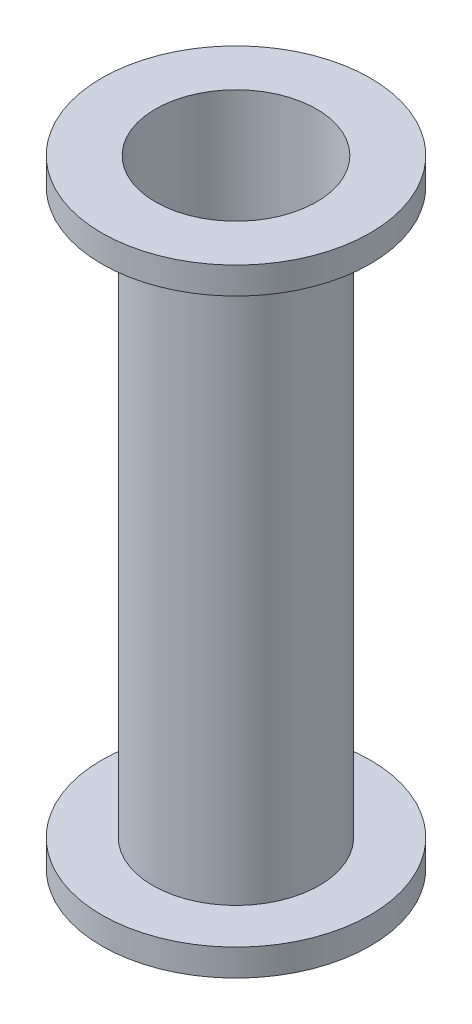
SolidWorks part; units mm, degrees
material "AISI 316 Annealed Stainless Steel Bar (SS)"
ref_plane "Front Plane" through (0, 0, 0) normal (0, 0, 1) x (1, 0, 0)
ref_plane "Top Plane" through (0, 0, 0) normal (0, 1, 0) x (1, 0, 0)
ref_plane "Right Plane" through (0, 0, 0) normal (1, 0, 0) x (0, 0, -1)
sketch "Sketch2" plane through (0, 0, 0) normal (0, 1, 0) x (1, 0, 0)
  circle A0 centre (0, 0) radius 38.1
  circle A1 centre (0, 0) radius 39.37
  dimension "D1" = 78.74
  dimension "D2" = 76.2
extrude "Base Cylinder" add sketch "Sketch2" along normal blind 292.1
sketch "Sketch3" plane through (0, 0, 0) normal (0, -1, 0) x (1, 0, 0)
  circle A0 centre (0, 0) radius 38.1
  circle A1 centre (0, 0) radius 63.5
  dimension "D1" = 127
extrude "Aft Flange" add sketch "Sketch3" against normal blind 12.7
sketch "Sketch4" plane through (0, 292.1, 0) normal (0, 1, 0) x (1, 0, 0)
  circle A0 centre (0, 0) radius 38.1
  circle A1 centre (0, 0) radius 63.5
  dimension "D1" = 127
extrude "Forward Flange" add sketch "Sketch4" against normal blind 12.7
fillet "Flange Fillet" [suppressed] radius 4.7625
sketch "Sketch6" plane through (0, 0, 0) normal (0, -1, 0) x (1, 0, 0)
  circle A0 centre (0, 0) radius 50.0761
  circle A1 centre (0, 0) radius 47.0027
  dimension "D1" = 100.1522
  dimension "D2" = 94.0054
extrude "Aft O-Ring" [suppressed] cut sketch "Sketch6" against normal blind 1.9812
sketch "Sketch7" plane through (0, 292.1, 0) normal (0, 1, 0) x (1, 0, 0)
  circle A0 centre (0, 0) radius 50.0761
  circle A1 centre (0, 0) radius 47.0027
  dimension "D1" = 100.1522
  dimension "D2" = 94.0054
extrude "Forward O-Ring" [suppressed] cut sketch "Sketch7" against normal blind 1.9812
sketch "Sketch For Bolt Holes" [suppressed] plane through (0, 0, 0) normal (0, -1, 0) x (1, 0, 0)
  circle A0 centre (-56.769, 0) radius 1.5875
  circle A1 centre (-49.1634, 28.3845) radius 1.5875
  circle A2 centre (-28.3845, 49.1634) radius 1.5875
  circle A3 centre (0, 56.769) radius 1.5875
  circle A4 centre (28.3845, 49.1634) radius 1.5875
  circle A5 centre (49.1634, 28.3845) radius 1.5875
  circle A6 centre (56.769, 0) radius 1.5875
  circle A7 centre (49.1634, -28.3845) radius 1.5875
  circle A8 centre (28.3845, -49.1634) radius 1.5875
  circle A9 centre (0, -56.769) radius 1.5875
  circle A10 centre (-28.3845, -49.1634) radius 1.5875
  circle A11 centre (-49.1634, -28.3845) radius 1.5875
  point P36 (0, 0)
  dimension "D2" = 3.175
  dimension "D1" = 56.769
  dimension "D3" = 12
hole_wizard "1/8 (0.125) Diameter Hole2" [suppressed] positions "Sketch8" profile "Sketch9" hole size "1/8" standard "ANSI Inch"
sketch "Sketch8" [suppressed] plane through (0, 0, 0) normal (0, -1, 0) x (-1, 0, 0)
  point P0 (-28.3845, -49.1634)
  point P3 (-49.1634, -28.3845)
  point P6 (-56.769, 0)
  point P9 (-49.1634, 28.3845)
  point P12 (-28.3845, 49.1634)
  point P15 (0, 56.769)
  point P18 (28.3845, 49.1634)
  point P21 (49.1634, 28.3845)
  point P24 (56.769, 0)
  point P27 (49.1634, -28.3845)
  point P30 (28.3845, -49.1634)
  point P33 (0, -56.769)
  point P36 (-28.3845, -49.1634)
  point P38 (-49.1634, -28.3845)
  point P40 (-56.769, 0)
sketch "Sketch9" plane through (28.3845, 0, 49.1634) normal (1, 0, 0) x (0, 0, -1)
  line L0 (0, 0) -> (0, 26.3539)
  line L1 (0, 26.3539) -> (1.5875, 25.4)
  line L2 (1.5875, 25.4) -> (1.5875, 0)
  line L5 (1.5875, 0) -> (0, 0)
  line L10 (0, 26.3539) -> (-1.5875, 25.4) construction
  line L11 (0, -6.35) -> (0, 107.95) construction
  dimension "Hole Dia." = 3.175
  dimension "Hole Depth" = 25.4
  dimension "Drill Angle" = 118
sketch "Dowel Hole Sketch" [suppressed] plane through (0, 0, 0) normal (0, -1, 0) x (1, 0, 0)
  line L0 (0, 0) -> (-56.769, 0) construction
  line L1 (0, 0) -> (-54.8346, -14.6929) construction
  line L2 (0, 0) -> (0, -56.769) construction
  line L3 (0, 0) -> (54.8346, 14.6929) construction
  circle A0 centre (0, 0) radius 56.769
  circle A1 centre (-54.8346, -14.6929) radius 4.6172
  circle A2 centre (54.8346, 14.6929) radius 3.4532
  dimension "D1" = 15
hole_wizard "1/4 (0.25) Press Dowel Hole1" [suppressed] positions "Sketch14" profile "Sketch12" hole size "1/4" standard "ANSI Inch"
sketch "Sketch14" [suppressed] plane through (0, 0, 0) normal (0, -1, 0) x (-1, 0, 0)
  point P0 (54.8346, 14.6929)
  point P3 (-54.8346, -14.6929)
sketch "Sketch12" plane through (-54.8346, 0, -14.6929) normal (1, 0, 0) x (0, 0, -1)
  line L0 (0, 0) -> (0, 8.2577)
  line L1 (0, 8.2577) -> (3.175, 6.35)
  line L2 (3.175, 6.35) -> (3.175, 0)
  line L5 (3.175, 0) -> (0, 0)
  line L10 (0, 8.2577) -> (-3.175, 6.35) construction
  line L11 (0, -6.35) -> (0, 107.95) construction
  dimension "Hole Dia." = 6.35
  dimension "Hole Depth" = 6.35
  dimension "Drill Angle" = 118
hole_wizard "1/8 (0.125) Diameter Hole4" [suppressed] positions "Sketch19" profile "Sketch21" hole size "1/8" standard "ANSI Inch"
sketch "Sketch19" [suppressed] plane through (0, 0, 0) normal (0, -1, 0) x (-1, 0, 0)
  point P0 (-54.8346, -14.6929)
  point P3 (54.8346, 14.6929)
sketch "Sketch21" plane through (54.8346, 0, 14.6929) normal (1, 0, 0) x (0, 0, -1)
  line L0 (0, 0) -> (0, 283.8423)
  line L1 (0, 283.8423) -> (1.5875, 283.8423)
  line L2 (1.5875, 283.8423) -> (1.5875, 0)
  line L5 (1.5875, 0) -> (0, 0)
  line L11 (0, -6.35) -> (0, 107.95) construction
  dimension "Thru Hole Dia." = 3.175
  dimension "Thru Hole Depth" = 283.8423
ref_plane "Hoop Mid-Plane" [suppressed] through (0, 146.05, 0) normal (0, 1, 0) x (1, 0, 0)
mirror "Forward Mirror BC and Pin" [suppressed] about plane through (0, 146.05, 0) normal (0, 1, 0)
ref_plane "PressureTapHolePlane" [suppressed] through (0, 0, 47.625) normal (0, 0, 1) x (1, 0, 0)
sketch "PressureTapHole" [suppressed] plane through (0, 0, 47.625) normal (0, 0, 1) x (1, 0, 0)
  line L1 (52.3875, 12.7) -> (-52.3875, 12.7) construction
  circle A0 centre (0, 31.75) radius 8.2246
  dimension "D1" = 19.05
hole_wizard "PressureTap1" [suppressed] positions "Sketch27" profile "Sketch28" legacy
sketch "Sketch27" [suppressed] plane through (0, 0, 47.625) normal (0, 0, 1) x (1, 0, 0)
  point P0 (0, 31.75)
sketch "Sketch28" plane through (0, 31.75, 47.625) normal (1, 0, 0) x (0, -1, 0)
  line L0 (0, 0) -> (0, 6.35)
  line L1 (0, 6.35) -> (0.3969, 6.35)
  line L2 (0.3969, 6.35) -> (0.3969, 1.5875)
  line L3 (0.3969, 1.5875) -> (1.5875, 1.5875)
  line L4 (1.5875, 1.5875) -> (1.5875, 0)
  line L5 (1.5875, 0) -> (0, 0)
  line L6 (0, 110) -> (0, -10) construction
  dimension "Diameter" = 0.7937
  dimension "Depth" = 6.35
  dimension "C-Bore Diameter" = 3.175
  dimension "C-Bore Depth" = 1.5875
ref_plane "PressureTapHole2Plane" [suppressed] through (0, 0, -47.625) normal (0, 0, 1) x (1, 0, 0)
sketch "PressureTapHole2" [suppressed] plane through (0, 0, -47.625) normal (0, 0, 1) x (1, 0, 0)
  line L0 (-52.3875, 279.4) -> (52.3875, 279.4) construction
  circle A0 centre (0, 254) radius 3.4964
  dimension "D1" = 25.4
hole_wizard "PressureTap2" [suppressed] positions "Sketch30" profile "Sketch31" legacy
sketch "Sketch30" [suppressed] plane through (0, 0, -47.625) normal (0, 0, 1) x (1, 0, 0)
  point P0 (0, 254)
sketch "Sketch31" plane through (0, 254, -47.625) normal (1, 0, 0) x (0, 1, 0)
  line L0 (0, 0) -> (0, 6.35)
  line L1 (0, 6.35) -> (0.7938, 6.35)
  line L2 (0.7938, 6.35) -> (0.7938, 3.175)
  line L3 (0.7938, 3.175) -> (1.5875, 3.175)
  line L4 (1.5875, 3.175) -> (1.5875, 0)
  line L5 (1.5875, 0) -> (0, 0)
  line L6 (0, 110) -> (0, -10) construction
  dimension "Diameter" = 1.5875
  dimension "Depth" = 6.35
  dimension "C-Bore Diameter" = 3.175
  dimension "C-Bore Depth" = 3.175
sketch "Sketch32" plane through (0, 292.1, 0) normal (0, 1, 0) x (1, 0, 0)
  line L0 (0, -69.85) -> (0, 69.85) construction
  line L1 (-64.2938, -36.7675) -> (-62.7062, -36.7675)
  line L2 (-64.2938, -36.7675) -> (-64.2938, 36.7675)
  line L3 (-64.2938, 36.7675) -> (-62.7062, 36.7675)
  line L4 (-62.7062, -36.7675) -> (-62.7062, 36.7675)
  line L5 (-64.2938, -36.7675) -> (-62.7062, 36.7675) construction
  line L6 (-64.2938, 36.7675) -> (-62.7062, -36.7675) construction
  line L7 (64.2938, 36.7675) -> (62.7062, 36.7675)
  line L8 (62.7062, -36.7675) -> (62.7062, 36.7675)
  line L9 (64.2938, -36.7675) -> (62.7062, -36.7675)
  line L10 (64.2938, -36.7675) -> (64.2938, 36.7675)
  circle A0 centre (0, 0) radius 63.5 construction
  point P0 (-63.5, 0)
  dimension "D1" = 1.5875
extrude "MillGrips" [suppressed] cut sketch "Sketch32" against normal through all both and the other way through all
